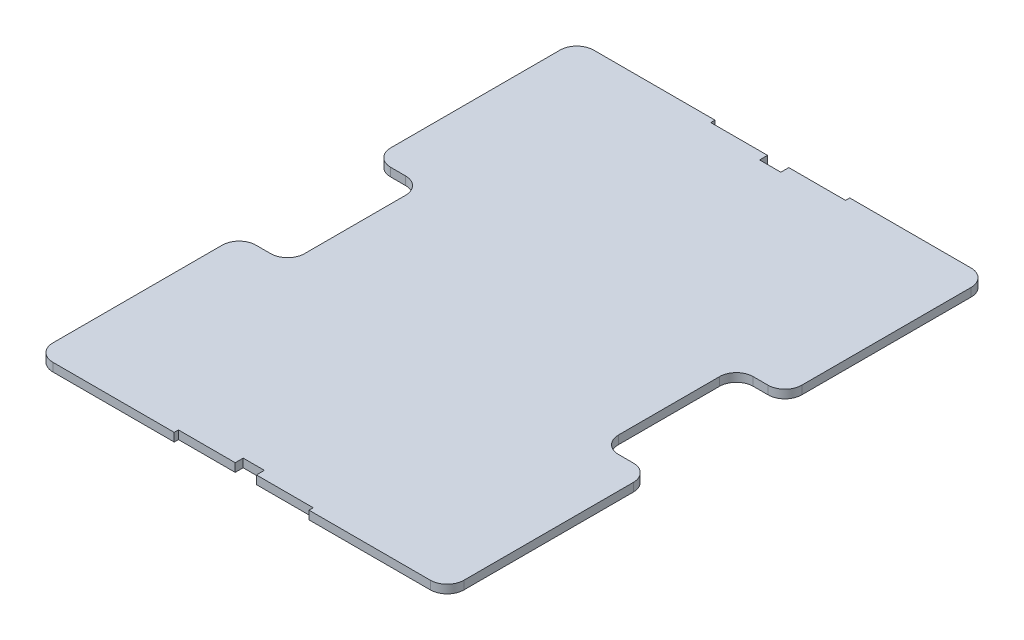
SolidWorks part; units mm, degrees
ref_plane "Front" through (0, 0, 0) normal (0, 0, 1) x (1, 0, 0)
ref_plane "Top" through (0, 0, 0) normal (0, 1, 0) x (1, 0, 0)
ref_plane "Right" through (0, 0, 0) normal (1, 0, 0) x (0, 0, -1)
sketch "Sketch3" plane through (0, 0, 0) normal (0, 1, 0) x (1, 0, 0)
  line L0 (-77.47, -25.4) -> (-77.47, -101.9175)
  line L1 (-77.47, 101.9175) -> (-25.4, 101.9175)
  line L2 (-77.47, 101.9175) -> (-77.47, 25.4)
  line L3 (-77.47, -101.9175) -> (-25.4, -101.9175)
  line L4 (77.47, 101.9175) -> (77.47, 25.4)
  line L6 (-25.4, 101.9175) -> (-25.4, 100.33)
  line L7 (-25.4, 100.33) -> (-4, 100.33)
  line L8 (25.4, 101.9175) -> (25.4, 100.33)
  line L9 (-77.47, 25.4) -> (-59.182, 25.4)
  line L11 (-77.47, -25.4) -> (-59.182, -25.4)
  line L12 (-59.182, 25.4) -> (-59.182, -25.4)
  line L13 (59.182, 25.4) -> (77.47, 25.4)
  line L14 (59.182, 25.4) -> (59.182, -25.4)
  line L15 (59.182, -25.4) -> (77.47, -25.4)
  line L17 (-25.4, -100.33) -> (-4, -100.33)
  line L18 (-25.4, -100.33) -> (-25.4, -101.9175)
  line L20 (25.4, -100.33) -> (25.4, -101.9175)
  line L21 (25.4, 101.9175) -> (77.47, 101.9175)
  line L22 (77.47, -25.4) -> (77.47, -101.9175)
  line L23 (25.4, -101.9175) -> (77.47, -101.9175)
  line L24 (4, -100.33) -> (25.4, -100.33)
  line L26 (-4, -100.33) -> (-4, -97.33)
  line L27 (-4, -97.33) -> (4, -97.33)
  line L28 (4, -100.33) -> (4, -97.33)
  line L29 (4, 100.33) -> (25.4, 100.33)
  line L31 (-4, 100.33) -> (-4, 97.33)
  line L32 (-4, 97.33) -> (4, 97.33)
  line L33 (4, 100.33) -> (4, 97.33)
  line L34 (0, 128.1548) -> (0, 38.8638) construction
  line L35 (-94.0002, 0) -> (-35.6003, 0) construction
  point P24 (0, -97.33)
  point P29 (-59.182, 0)
  point P32 (0, 97.33)
  dimension "D1" = 50.8
  dimension "D2" = 50.8
  dimension "D3" = 50.8
  dimension "D4" = 50.8
  dimension "D5" = 1.5875
  dimension "D6" = 18.288
  dimension "D7" = 18.288
  dimension "D8" = 1.5875
  dimension "D9" = 154.94
  dimension "D10" = 203.835
  dimension "D19" = 8
  dimension "D20" = 3
  dimension "D21" = 3
  dimension "D22" = 8
extrude "Boss-Extrude3" add sketch "Sketch3" along normal mid plane 3.175
fillet "Fillet1" radius 6.35 12 edges at (77.47, 0, -25.4) (59.182, 0, -25.4) (59.182, 0, 25.4) (77.47, 0, 25.4) (-59.182, 0, -25.4) (-77.47, 0, -25.4) (-59.182, 0, 25.4) (-77.47, 0, 25.4) (-77.47, 0, -101.9175) (77.47, 0, -101.9175) (77.47, 0, 101.9175) (-77.47, 0, 101.9175)
